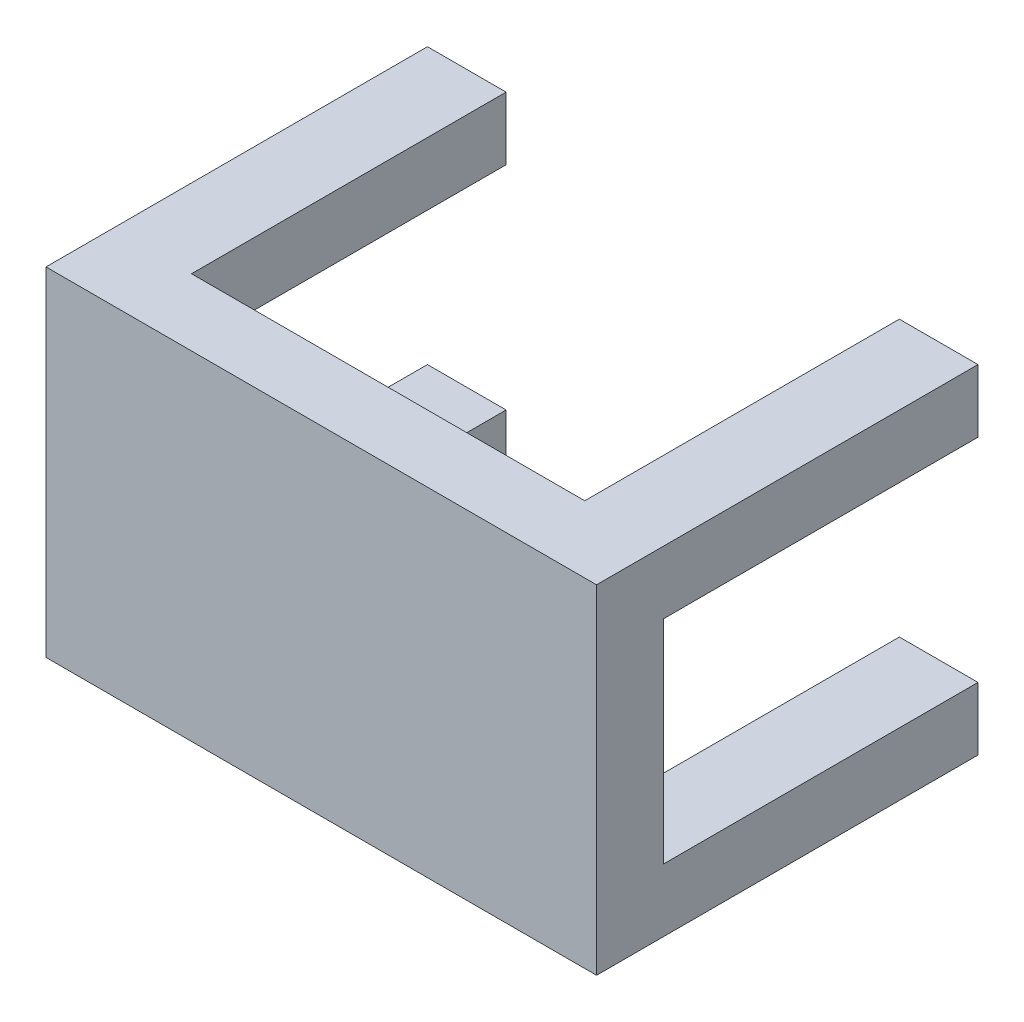
SolidWorks part; units mm, degrees
ref_plane "前视基准面" through (0, 0, 0) normal (0, 0, 1) x (1, 0, 0)
ref_plane "上视基准面" through (0, 0, 0) normal (0, 1, 0) x (1, 0, 0)
ref_plane "右视基准面" through (0, 0, 0) normal (1, 0, 0) x (0, 0, -1)
sketch "草图1" plane through (0, 0, 0) normal (0, 0, 1) x (1, 0, 0)
  line L1 (-35, -21.5) -> (35, -21.5)
  line L2 (-35, -21.5) -> (-35, 21.5)
  line L3 (-35, 21.5) -> (35, 21.5)
  line L4 (35, -21.5) -> (35, 21.5)
  line L5 (-35, -21.5) -> (35, 21.5) construction
  line L6 (-35, 21.5) -> (35, -21.5) construction
  point P0 (0, 0)
  dimension "D1" = 70
  dimension "D2" = 43
extrude "凸台-拉伸1" add sketch "草图1" along normal blind 48.5
sketch "草图2" plane through (0, 0, 0) normal (0, 0, -1) x (-1, 0, 0)
  line L0 (-25, 13.5) -> (-25, 21.5)
  line L1 (-25, -13.5) -> (25, -13.5)
  line L2 (-25, -13.5) -> (-25, 13.5)
  line L3 (-25, 13.5) -> (25, 13.5)
  line L4 (25, -13.5) -> (25, 13.5)
  line L5 (-25, -13.5) -> (25, 13.5) construction
  line L6 (-25, 13.5) -> (25, -13.5) construction
  line L7 (-35, 21.5) -> (35, 21.5) construction
  line L8 (-25, 13.5) -> (-35, 13.5)
  line L9 (-35, -21.5) -> (-35, 21.5) construction
  line L10 (-35, 13.5) -> (-35, -13.5)
  line L11 (-35, -13.5) -> (-25, -13.5)
  line L12 (-25, -13.5) -> (-25, -21.5)
  line L13 (35, -21.5) -> (-35, -21.5) construction
  line L14 (-25, -21.5) -> (25, -21.5)
  line L15 (25, -21.5) -> (25, -13.5)
  line L16 (35, -13.5) -> (35, 13.5)
  line L17 (35, 21.5) -> (35, -21.5) construction
  line L18 (35, 13.5) -> (25, 13.5)
  line L19 (25, 21.5) -> (-25, 21.5)
  line L20 (25, -13.5) -> (35, -13.5)
  line L21 (25, 21.5) -> (25, 13.5)
  point P0 (0, 0)
  line M1 (-35, 21.5) -> (-35, -21.5)
  line M2 (-35, -21.5) -> (35, -21.5)
  line M3 (35, -21.5) -> (35, 21.5)
  line M4 (35, 21.5) -> (-35, 21.5)
  dimension "D1" = 27
  dimension "D2" = 50
extrude "切除-拉伸1" cut sketch "草图2" against normal blind 40 contours L1 L4 L3 L2 | L15 L1 L12 M2 | L11 L2 L8 M1 | L21 L0 L3 M4 | L4 L20 L18 M3
hole_wizard "M3 螺纹孔1" positions "草图4" profile "草图5" tap size "M3" standard "GB"
sketch "草图4" plane through (0, 0, 0) normal (0, 0, -1) x (-1, 0, 0)
  line L0 (-25, 13.5) -> (-35, 13.5) construction
  line L3 (-25, 13.5) -> (-25, 21.5) construction
  line L4 (25, 21.5) -> (25, 13.5) construction
  line L5 (-35, -13.5) -> (-25, -13.5) construction
  point P0 (-30, 17.5)
  point P2 (30, 17.5)
  point P4 (30, -17.5)
  point P6 (-30, -17.5)
  point P17 (0, 0)
  point P20 (0, 0)
  point P21 (-30, -17.2188)
  dimension "D1" = 4
  dimension "D2" = 5
  dimension "D3" = 5
  dimension "D4" = 4
sketch "草图5" plane through (30, 17.5, 0) normal (1, 0, 0) x (0, 1, 0)
  line L0 (0, 0) -> (0, 15.7511)
  line L1 (0, 15.7511) -> (1.25, 15)
  line L2 (1.25, 15) -> (1.25, 0)
  line L5 (1.25, 0) -> (0, 0)
  line L10 (0, 15.7511) -> (-1.25, 15) construction
  line L11 (0, -6.35) -> (0, 107.95) construction
  dimension "螺纹孔钻头直径" = 2.5
  dimension "螺纹孔钻头深度" = 15
  dimension "导头角度" = 118
cosmetic thread "孔螺蚊线1" parameters "D1"=10, "D2"=3
cosmetic thread "孔螺蚊线2" parameters "D1"=10, "D2"=3
cosmetic thread "孔螺蚊线3" parameters "D1"=10, "D2"=3
cosmetic thread "孔螺蚊线4" parameters "D1"=10, "D2"=3
